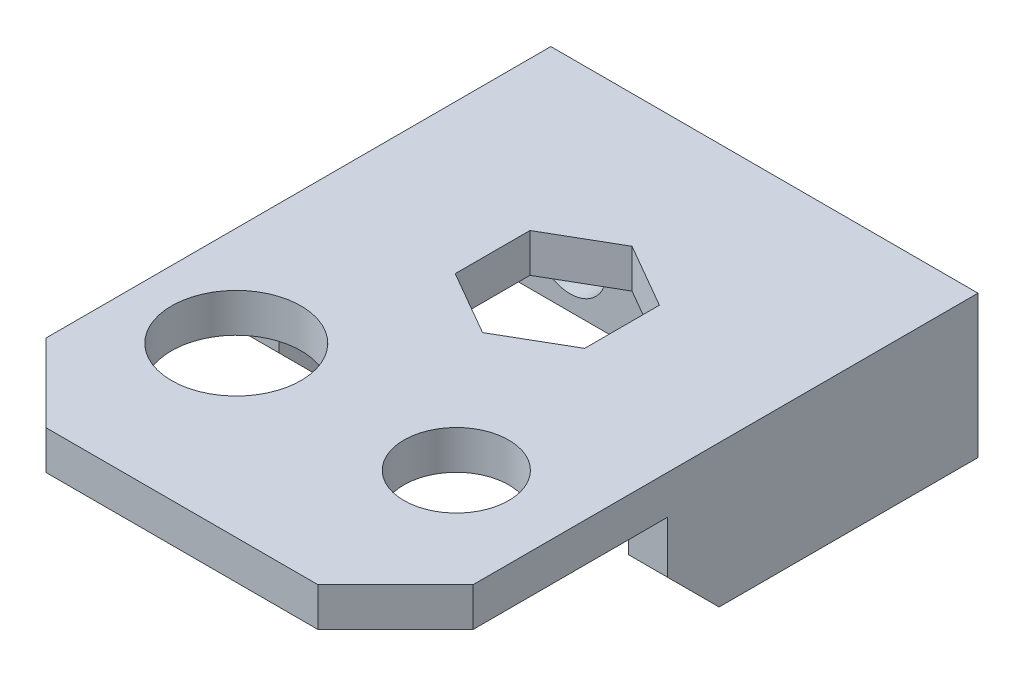
SolidWorks part; units mm, degrees
ref_plane "Alzado" through (0, 0, 0) normal (0, 0, 1) x (1, 0, 0)
ref_plane "Planta" through (0, 0, 0) normal (0, 1, 0) x (1, 0, 0)
ref_plane "Vista lateral" through (0, 0, 0) normal (1, 0, 0) x (0, 0, -1)
sketch "Croquis1" plane through (0, 0, 0) normal (0, 1, 0) x (1, 0, 0)
  line L0 (0, 32) -> (25.3011, 32)
  line L1 (0, 0) -> (0, 32) construction
  line L2 (25.3011, 32) -> (25.3011, -7)
  line L3 (19.3011, -13) -> (-1.6989, -13)
  line L4 (-7.6989, -7) -> (-7.6989, 32)
  line L5 (-7.6989, 32) -> (0, 32)
  line L6 (-1.6989, -13) -> (-7.6989, -7)
  line L7 (25.3011, -7) -> (19.3011, -13)
  circle A0 centre (0, 0) radius 5
  circle A1 centre (17, 0) radius 4.05
  point P7 (25.3011, -13)
  point P9 (-7.6989, -13)
  dimension "D1" = 10
  dimension "D2" = 8.1
  dimension "D3" = 17
  dimension "D4" = 32
  dimension "D5" = 45
  dimension "D6" = 33
  dimension "D7" = 7.6989
extrude "Saliente-Extruir1" add sketch "Croquis1" along normal blind 3
sketch "Croquis5" plane through (0, 0, 0) normal (0, -1, 0) x (1, 0, 0)
  line L0 (-7.6989, -8) -> (-7.6989, -29)
  line L1 (-7.6989, -32) -> (-7.6989, 7) construction
  line L2 (-7.6989, -8) -> (-4.6989, -8)
  line L3 (-4.6989, -8) -> (-4.6989, -29)
  line L5 (-4.6989, -29) -> (-7.6989, -29)
  dimension "D1" = 3
  dimension "D2" = 21
  dimension "D5" = 3
extrude "Saliente-Extruir3" add sketch "Croquis5" along normal blind 8
sketch "Croquis7" plane through (-7.6989, 0, 0) normal (-1, 0, 0) x (0, 0, 1)
  line L0 (-8, -8) -> (-12, -8)
  line L2 (-12, -8) -> (-8, -4)
  line L4 (-8, -4) -> (-8, -8)
  dimension "D1" = 4
  dimension "D2" = 4
  dimension "D3" = 5.6569
sketch "Croquis11" plane through (0, 0, 0) normal (0, -1, 0) x (1, 0, 0)
  line L0 (25.3011, -29) -> (22.3011, -29)
  line L2 (22.3011, -29) -> (22.3011, -8)
  line L3 (22.3011, -8) -> (25.3011, -8)
  line L4 (25.3011, 7) -> (25.3011, -32) construction
  line L5 (25.3011, -8) -> (25.3011, -29)
  dimension "D1" = 21
  dimension "D2" = 3
  dimension "D3" = 3
  dimension "D4" = 21
extrude "Saliente-Extruir6" add sketch "Croquis11" along normal blind 8
extrude "Cortar-Extruir3" cut sketch "Croquis7" against normal through all
sketch "Croquis9" plane through (0, 3, 0) normal (0, 1, 0) x (1, 0, 0)
  line L0 (-7.6989, 32) -> (-7.6989, -7) construction
  line L1 (8.8011, 10.2265) -> (13.8011, 13.1132)
  line L2 (13.8011, 13.1132) -> (13.8011, 18.8868)
  line L3 (13.8011, 18.8868) -> (8.8011, 21.7735)
  line L4 (8.8011, 21.7735) -> (3.8011, 18.8868)
  line L5 (3.8011, 18.8868) -> (3.8011, 13.1132)
  line L6 (3.8011, 13.1132) -> (8.8011, 10.2265)
  circle A0 centre (8.8011, 16) radius 5 construction
  dimension "D3" = 10
  dimension "D1" = 16.5
  dimension "D2" = 13
extrude "Cortar-Extruir4" cut sketch "Croquis9" against normal blind 3
sketch "Croquis13" plane through (0, 0, 0) normal (0, -1, 0) x (1, 0, 0)
  line L0 (-4.6989, -29) -> (-4.6989, -26)
  line L1 (25.3011, -29) -> (25.3011, -32) construction
  line L2 (25.3011, -32) -> (-7.6989, -32) construction
  line L3 (-7.6989, -32) -> (-7.6989, -29) construction
  line L4 (25.3011, -29) -> (25.3011, -32)
  line L5 (25.3011, -32) -> (-7.6989, -32)
  line L6 (-7.6989, -32) -> (-7.6989, -29)
  line L7 (-4.6989, -29) -> (-4.6989, -8) construction
  line L8 (-4.6989, -26) -> (22.3011, -26)
  line L9 (22.3011, -8) -> (22.3011, -29) construction
  line L10 (22.3011, -26) -> (22.3011, -29)
  line L11 (22.3011, -29) -> (25.3011, -29)
  line L12 (-7.6989, -29) -> (-4.6989, -29)
  dimension "D1" = 6
extrude "Saliente-Extruir8" add sketch "Croquis13" along normal up to surface (8 mm away) up to face at (-6.1989, -8, -20.5)
sketch "Croquis15" plane through (0, 0, -26) normal (0, 0, 1) x (1, 0, 0)
  circle A0 centre (-0.1989, -4) radius 1.55
  circle A1 centre (17.8011, -4) radius 1.55
  dimension "D1" = 3.1
  dimension "D2" = 3.1
  dimension "D3" = 18
  dimension "D4" = 4.5
  dimension "D5" = 4
extrude "Cortar-Extruir6" cut sketch "Croquis15" against normal through all
sketch "Croquis16" plane through (0, 0, -26) normal (0, 0, 1) x (1, 0, 0)
  circle A0 centre (17.8011, -4) radius 1.55 construction
  circle A1 centre (-0.1989, -4) radius 1.55 construction
  circle A2 centre (17.8011, -4) radius 1.55
  circle A3 centre (-0.1989, -4) radius 1.55
  circle A4 centre (-0.1989, -4) radius 2.8
  circle A5 centre (17.8011, -4) radius 2.8
  dimension "D1" = 5.6
  dimension "D2" = 5.6
extrude "Cortar-Extruir7" cut sketch "Croquis16" against normal blind 3
